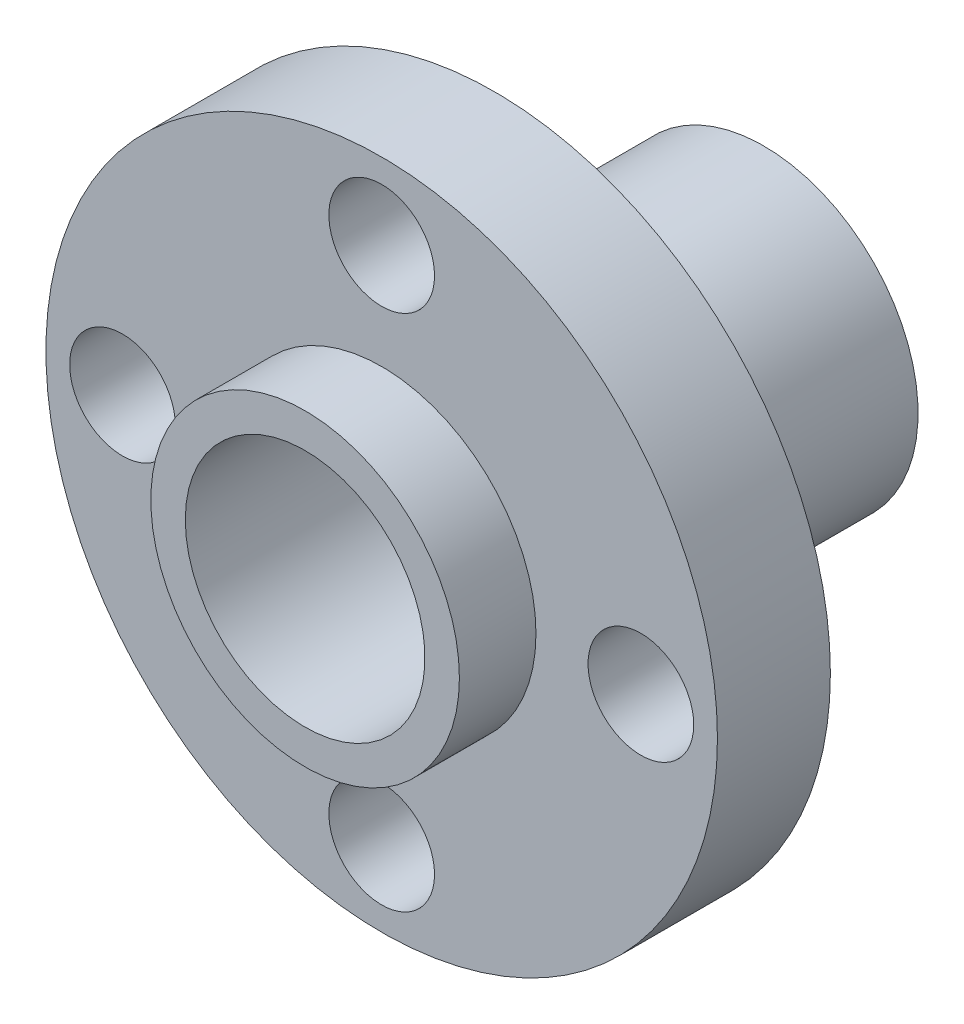
SolidWorks part; units mm, degrees
ref_plane "Front Plane" through (0, 0, 0) normal (0, 0, 1) x (1, 0, 0)
ref_plane "Top Plane" through (0, 0, 0) normal (0, 1, 0) x (1, 0, 0)
ref_plane "Right Plane" through (0, 0, 0) normal (1, 0, 0) x (0, 0, -1)
sketch "Sketch1" plane through (0, 0, 0) normal (0, 0, 1) x (1, 0, 0)
  circle A0 centre (0, 0) radius 11.1379
  dimension "D1" = 22.2758
extrude "Boss-Extrude1" add sketch "Sketch1" along normal blind 3.7465
sketch "Sketch2" plane through (0, 0, 0) normal (0, 0, -1) x (-1, 0, 0)
  circle A0 centre (0, 0) radius 5.1181
  dimension "D1" = 10.2362
extrude "Boss-Extrude2" add sketch "Sketch2" along normal blind 8.9281 contours A0
sketch "Sketch3" plane through (0, 0, 3.7465) normal (0, 0, 1) x (1, 0, 0)
  circle A0 centre (0, 0) radius 5.1181
  dimension "D1" = 10.2362
extrude "Boss-Extrude3" add sketch "Sketch3" along normal blind 2.54
sketch "Sketch4" plane through (0, 0, -8.9281) normal (0, 0, -1) x (-1, 0, 0)
  circle A0 centre (0, 0) radius 3.9751
  dimension "D1" = 7.9502
extrude "Cut-Extrude1" cut sketch "Sketch4" against normal through all
sketch "Sketch5" plane through (0, 0, 3.7465) normal (0, 0, 1) x (1, 0, 0)
  line L0 (0, 0) -> (0, 11.1379) construction
  line L1 (0, 0) -> (11.1379, 0) construction
  line L2 (0, 0) -> (0, -11.1379) construction
  line L3 (0, 0) -> (-11.1379, 0) construction
  circle A0 centre (0, 0) radius 11.1379 construction
  circle A1 centre (0, 8.5979) radius 1.7526
  circle A5 centre (8.5979, 0) radius 1.7526
  circle A6 centre (0, -8.5979) radius 1.7526
  circle A7 centre (-8.5979, 0) radius 1.7526
  point P17 (0, 0)
  point P21 (0, 0)
  dimension "D1" = 3.5052
  dimension "D2" = 8.5979
  dimension "D3" = 4
extrude "Cut-Extrude2" cut sketch "Sketch5" against normal through all
